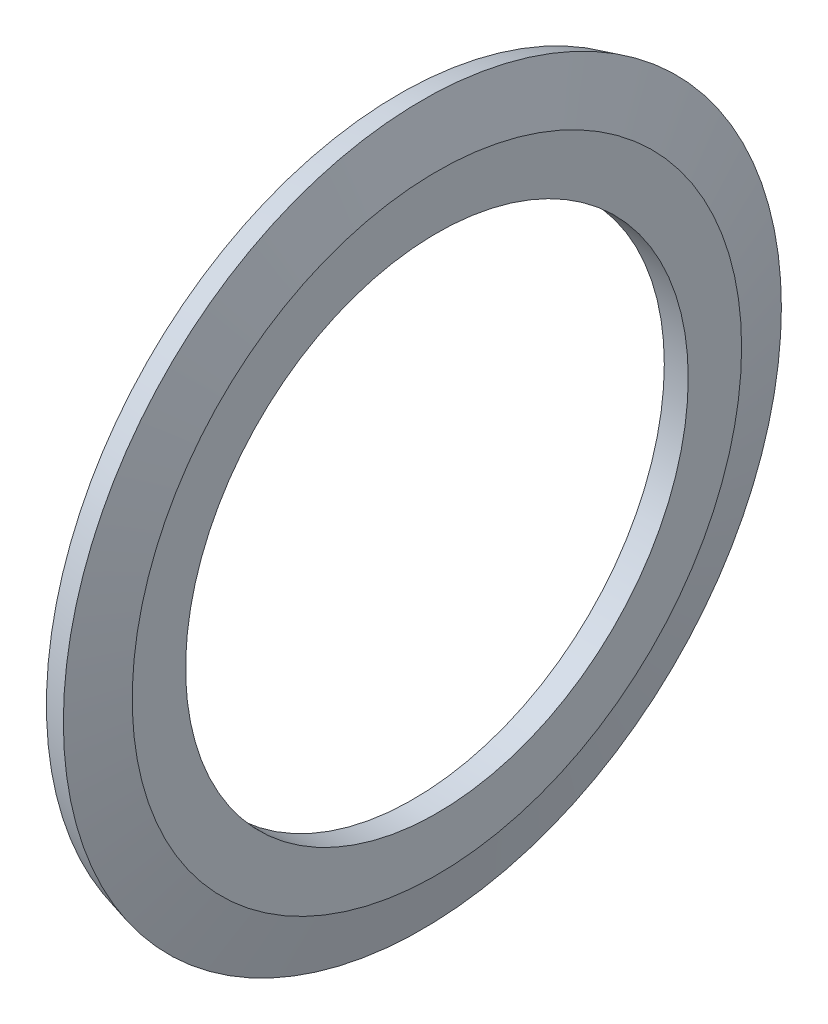
SolidWorks part; units mm, degrees
ref_plane "Front Plane" through (0, 0, 0) normal (0, 0, 1) x (1, 0, 0)
ref_plane "Top Plane" through (0, 0, 0) normal (0, 1, 0) x (1, 0, 0)
ref_plane "Right Plane" through (0, 0, 0) normal (1, 0, 0) x (0, 0, -1)
sketch "Sketch1" plane through (0, 0, 0) normal (0, 0, 1) x (1, 0, 0)
  line L0 (1, 10.5) -> (0, 10.5)
  line L1 (0, 10.5) -> (0, 12.5983)
  line L2 (1, 10.5) -> (1, 12.73)
  line L3 (1, 12.73) -> (0.3918, 15)
  line L4 (0.3918, 15) -> (-0.5742, 14.7412)
  line L5 (-0.5742, 14.7412) -> (0, 12.5983)
  line L6 (1, 0) -> (0, 0) construction
  dimension "D1" = 1
  dimension "D2" = 15
  dimension "E" = 21
  dimension "P.D." = 25.46
  dimension "F_1" = 30
revolve "Revolve1" add sketch "Sketch1" angle 360 about L6
sketch "Sketch2" [suppressed] plane through (0, 0, 0) normal (0, 0, 1) x (1, 0, 0)
  line L0 (-0.4389, 0) -> (0, 0) construction
  line L1 (-0.4389, 18) -> (1, 18)
  line L2 (-0.4389, 18) -> (-0.4389, 16.5)
  line L3 (-0.4389, 16.5) -> (1, 16.5)
  line L4 (1, 18) -> (1, 16.5)
  line L7 (1, -16.235) -> (1, 16.235) construction
  line L8 (-0.4389, 17.7412) -> (-0.4389, -17.7412) construction
  dimension "FC" = 40
revolve "Cut-Revolve1" [suppressed] cut sketch "Sketch2" angle 360 about L0
